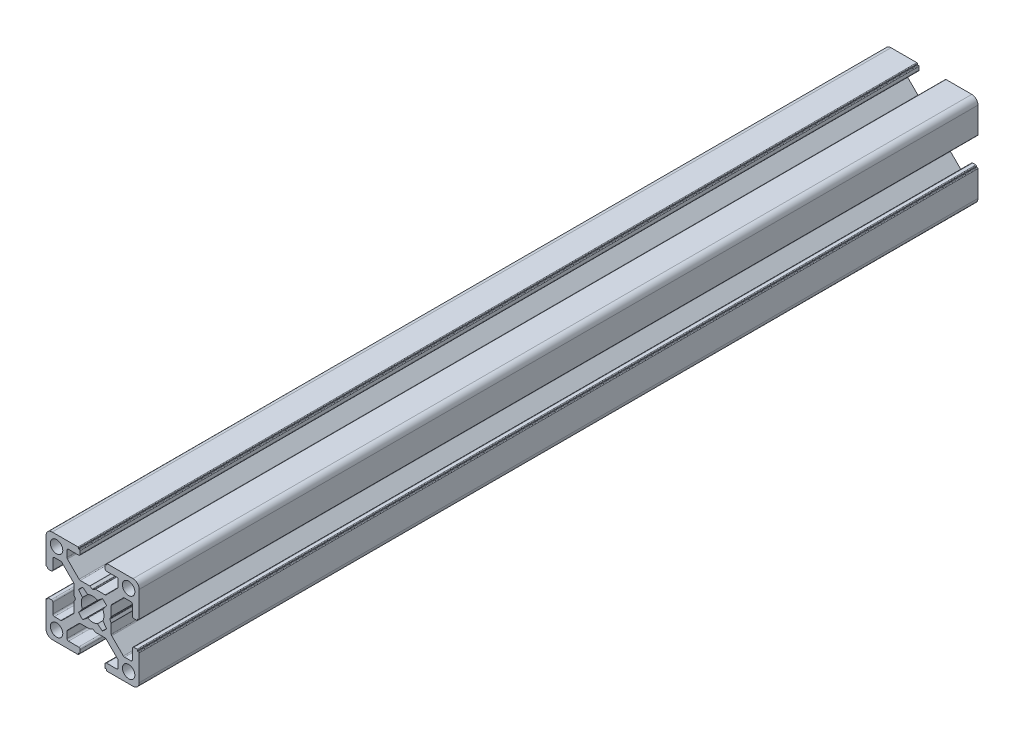
SolidWorks part; units mm, degrees
ref_plane "Alzado" through (0, 0, 0) normal (0, 0, 1) x (1, 0, 0)
ref_plane "Planta" through (0, 0, 0) normal (0, 1, 0) x (1, 0, 0)
ref_plane "Vista lateral" through (0, 0, 0) normal (1, 0, 0) x (0, 0, -1)
ref_plane "Plano1" through (0, 0, 1000) normal (0, 0, 1) x (1, 0, 0)
sketch "Croquis1" plane through (0, 0, 1000) normal (0, 0, 1) x (1, 0, 0)
  line L16 (-7.8359, -10.4816) -> (-6.3001, -11.7194)
  line L17 (-3.0999, -11.7194) -> (-1.5641, -10.4816)
  line L18 (-0.1947, -11.8453) -> (-1.4194, -13.3999)
  line L19 (-1.4194, -16.6001) -> (-0.1947, -18.1547)
  line L20 (-1.5641, -19.5184) -> (-3.0999, -18.2806)
  line L21 (-6.3001, -18.2806) -> (-7.8359, -19.5184)
  line L22 (-9.2053, -18.1547) -> (-7.9806, -16.6001)
  line L23 (-7.9806, -13.3999) -> (-9.2053, -11.8453)
  line L24 (9.8, -10.5) -> (10.1, -10.5)
  line L25 (10.3, -10.3) -> (10.3, -2)
  line L26 (8.3, 0) -> (0, 0)
  line L27 (-0.2, -0.2) -> (-0.2, -0.5)
  line L28 (-0.2, -0.5) -> (-0.5, -0.5)
  line L29 (-0.7, -0.7) -> (-0.7, -1.7)
  line L30 (-0.2, -2.2) -> (3.05, -2.2)
  line L31 (3.55, -2.7) -> (3.55, -4.7431)
  line L32 (3.4037, -5.0964) -> (-0.3491, -8.8534)
  line L33 (-0.7028, -9) -> (-3.7468, -9)
  line L34 (-3.8462, -9.0264) -> (-4.6006, -9.4583)
  line L35 (-4.7994, -9.4583) -> (-5.5538, -9.0264)
  line L36 (-5.6532, -9) -> (-8.6972, -9)
  line L37 (-9.0509, -8.8534) -> (-12.8037, -5.0964)
  line L38 (-12.95, -4.7431) -> (-12.95, -2.7)
  line L39 (-12.45, -2.2) -> (-9.2, -2.2)
  line L40 (-8.7, -1.7) -> (-8.7, -0.7)
  line L41 (-8.9, -0.5) -> (-9.2, -0.5)
  line L42 (-9.2, -0.5) -> (-9.2, -0.2)
  line L43 (-9.4, 0) -> (-17.7, 0)
  line L44 (-19.7, -2) -> (-19.7, -10.3)
  line L45 (-19.5, -10.5) -> (-19.2, -10.5)
  line L46 (-19.2, -10.5) -> (-19.2, -10.8)
  line L47 (-19, -11) -> (-18, -11)
  line L48 (-17.5, -10.5) -> (-17.5, -7.25)
  line L49 (-17, -6.75) -> (-14.9569, -6.75)
  line L50 (-14.6036, -6.8963) -> (-10.8466, -10.6491)
  line L51 (-10.7, -11.0028) -> (-10.7, -14.0468)
  line L52 (-10.6736, -14.1462) -> (-10.2417, -14.9006)
  line L53 (-10.2417, -15.0994) -> (-10.6736, -15.8538)
  line L54 (-10.7, -15.9532) -> (-10.7, -18.9972)
  line L55 (-10.8466, -19.3509) -> (-14.6036, -23.1037)
  line L56 (-14.9569, -23.25) -> (-17, -23.25)
  line L57 (-17.5, -22.75) -> (-17.5, -19.5)
  line L58 (-18, -19) -> (-19, -19)
  line L59 (-19.2, -19.2) -> (-19.2, -19.5)
  line L60 (-19.2, -19.5) -> (-19.5, -19.5)
  line L61 (-19.7, -19.7) -> (-19.7, -28)
  line L62 (-17.7, -30) -> (-9.4, -30)
  line L63 (-9.2, -29.8) -> (-9.2, -29.5)
  line L64 (-9.2, -29.5) -> (-8.9, -29.5)
  line L65 (-8.7, -29.3) -> (-8.7, -28.3)
  line L66 (-9.2, -27.8) -> (-12.45, -27.8)
  line L67 (-12.95, -27.3) -> (-12.95, -25.2569)
  line L68 (-12.8037, -24.9036) -> (-9.0509, -21.1466)
  line L69 (-8.6972, -21) -> (-5.6532, -21)
  line L70 (-5.5538, -20.9736) -> (-4.7994, -20.5417)
  line L71 (-4.6006, -20.5417) -> (-3.8462, -20.9736)
  line L72 (-3.7468, -21) -> (-0.7028, -21)
  line L73 (-0.3491, -21.1466) -> (3.4037, -24.9036)
  line L74 (3.55, -25.2569) -> (3.55, -27.3)
  line L75 (3.05, -27.8) -> (-0.2, -27.8)
  line L76 (-0.7, -28.3) -> (-0.7, -29.3)
  line L77 (-0.5, -29.5) -> (-0.2, -29.5)
  line L78 (-0.2, -29.5) -> (-0.2, -29.8)
  line L79 (0, -30) -> (8.3, -30)
  line L80 (10.3, -28) -> (10.3, -19.7)
  line L81 (10.1, -19.5) -> (9.8, -19.5)
  line L82 (9.8, -19.5) -> (9.8, -19.2)
  line L83 (9.6, -19) -> (8.6, -19)
  line L84 (8.1, -19.5) -> (8.1, -22.75)
  line L85 (7.6, -23.25) -> (5.5569, -23.25)
  line L86 (5.2036, -23.1037) -> (1.4466, -19.3509)
  line L87 (1.3, -18.9972) -> (1.3, -15.9532)
  line L88 (1.2736, -15.8538) -> (0.8417, -15.0994)
  line L89 (0.8417, -14.9006) -> (1.2736, -14.1462)
  line L90 (1.3, -14.0468) -> (1.3, -11.0028)
  line L91 (1.4466, -10.6491) -> (5.2036, -6.8963)
  line L92 (5.5569, -6.75) -> (7.6, -6.75)
  line L93 (8.1, -7.25) -> (8.1, -10.5)
  line L94 (8.6, -11) -> (9.6, -11)
  line L95 (9.8, -10.8) -> (9.8, -10.5)
  line L96 (8, -2.3) -> (5.8, -4.5) construction
  line L97 (-15.2, -2.3) -> (-17.4, -4.5) construction
  line L98 (-4.7, -15) -> (6.9, -15) construction
  arc A16 (-9.2053, -11.8453) -> (-7.8359, -10.4816) centre (-4.7, -15) cw
  arc A17 (-6.3001, -11.7194) -> (-3.0999, -11.7194) centre (-4.7, -15) cw
  arc A18 (-1.5641, -10.4816) -> (-0.1947, -11.8453) centre (-4.7, -15) cw
  arc A19 (-1.4194, -13.3999) -> (-1.4194, -16.6001) centre (-4.7, -15) cw
  arc A20 (-0.1947, -18.1547) -> (-1.5641, -19.5184) centre (-4.7, -15) cw
  arc A21 (-3.0999, -18.2806) -> (-6.3001, -18.2806) centre (-4.7, -15) cw
  arc A22 (-7.8359, -19.5184) -> (-9.2053, -18.1547) centre (-4.7, -15) cw
  arc A23 (-7.9806, -16.6001) -> (-7.9806, -13.3999) centre (-4.7, -15) cw
  arc A24 (10.1, -10.5) -> (10.3, -10.3) centre (10.1, -10.3) ccw
  arc A25 (10.3, -2) -> (8.3, 0) centre (8.3, -2) ccw
  arc A26 (0, 0) -> (-0.2, -0.2) centre (0, -0.2) ccw
  arc A27 (-0.5, -0.5) -> (-0.7, -0.7) centre (-0.5, -0.7) ccw
  arc A28 (-0.7, -1.7) -> (-0.2, -2.2) centre (-0.2, -1.7) ccw
  arc A29 (3.05, -2.2) -> (3.55, -2.7) centre (3.05, -2.7) cw
  arc A30 (3.55, -4.7431) -> (3.4037, -5.0964) centre (3.05, -4.7431) cw
  arc A31 (-0.3491, -8.8534) -> (-0.7028, -9) centre (-0.7028, -8.5) cw
  arc A32 (-3.7468, -9) -> (-3.8462, -9.0264) centre (-3.7468, -9.2) ccw
  arc A33 (-4.6006, -9.4583) -> (-4.7994, -9.4583) centre (-4.7, -9.2847) cw
  arc A34 (-5.5538, -9.0264) -> (-5.6532, -9) centre (-5.6532, -9.2) ccw
  arc A35 (-8.6972, -9) -> (-9.0509, -8.8534) centre (-8.6972, -8.5) cw
  arc A36 (-12.8037, -5.0964) -> (-12.95, -4.7431) centre (-12.45, -4.7431) cw
  arc A37 (-12.95, -2.7) -> (-12.45, -2.2) centre (-12.45, -2.7) cw
  arc A38 (-9.2, -2.2) -> (-8.7, -1.7) centre (-9.2, -1.7) ccw
  arc A39 (-8.7, -0.7) -> (-8.9, -0.5) centre (-8.9, -0.7) ccw
  arc A40 (-9.2, -0.2) -> (-9.4, 0) centre (-9.4, -0.2) ccw
  arc A41 (-17.7, 0) -> (-19.7, -2) centre (-17.7, -2) ccw
  arc A42 (-19.7, -10.3) -> (-19.5, -10.5) centre (-19.5, -10.3) ccw
  arc A43 (-19.2, -10.8) -> (-19, -11) centre (-19, -10.8) ccw
  arc A44 (-18, -11) -> (-17.5, -10.5) centre (-18, -10.5) ccw
  arc A45 (-17.5, -7.25) -> (-17, -6.75) centre (-17, -7.25) cw
  arc A46 (-14.9569, -6.75) -> (-14.6036, -6.8963) centre (-14.9569, -7.25) cw
  arc A47 (-10.8466, -10.6491) -> (-10.7, -11.0028) centre (-11.2, -11.0028) cw
  arc A48 (-10.7, -14.0468) -> (-10.6736, -14.1462) centre (-10.5, -14.0468) ccw
  arc A49 (-10.2417, -14.9006) -> (-10.2417, -15.0994) centre (-10.4153, -15) cw
  arc A50 (-10.6736, -15.8538) -> (-10.7, -15.9532) centre (-10.5, -15.9532) ccw
  arc A51 (-10.7, -18.9972) -> (-10.8466, -19.3509) centre (-11.2, -18.9972) cw
  arc A52 (-14.6036, -23.1037) -> (-14.9569, -23.25) centre (-14.9569, -22.75) cw
  arc A53 (-17, -23.25) -> (-17.5, -22.75) centre (-17, -22.75) cw
  arc A54 (-17.5, -19.5) -> (-18, -19) centre (-18, -19.5) ccw
  arc A55 (-19, -19) -> (-19.2, -19.2) centre (-19, -19.2) ccw
  arc A56 (-19.5, -19.5) -> (-19.7, -19.7) centre (-19.5, -19.7) ccw
  arc A57 (-19.7, -28) -> (-17.7, -30) centre (-17.7, -28) ccw
  arc A58 (-9.4, -30) -> (-9.2, -29.8) centre (-9.4, -29.8) ccw
  arc A59 (-8.9, -29.5) -> (-8.7, -29.3) centre (-8.9, -29.3) ccw
  arc A60 (-8.7, -28.3) -> (-9.2, -27.8) centre (-9.2, -28.3) ccw
  arc A61 (-12.45, -27.8) -> (-12.95, -27.3) centre (-12.45, -27.3) cw
  arc A62 (-12.95, -25.2569) -> (-12.8037, -24.9036) centre (-12.45, -25.2569) cw
  arc A63 (-9.0509, -21.1466) -> (-8.6972, -21) centre (-8.6972, -21.5) cw
  arc A64 (-5.6532, -21) -> (-5.5538, -20.9736) centre (-5.6532, -20.8) ccw
  arc A65 (-4.7994, -20.5417) -> (-4.6006, -20.5417) centre (-4.7, -20.7153) cw
  arc A66 (-3.8462, -20.9736) -> (-3.7468, -21) centre (-3.7468, -20.8) ccw
  arc A67 (-0.7028, -21) -> (-0.3491, -21.1466) centre (-0.7028, -21.5) cw
  arc A68 (3.4037, -24.9036) -> (3.55, -25.2569) centre (3.05, -25.2569) cw
  arc A69 (3.55, -27.3) -> (3.05, -27.8) centre (3.05, -27.3) cw
  arc A70 (-0.2, -27.8) -> (-0.7, -28.3) centre (-0.2, -28.3) ccw
  arc A71 (-0.7, -29.3) -> (-0.5, -29.5) centre (-0.5, -29.3) ccw
  arc A72 (-0.2, -29.8) -> (0, -30) centre (0, -29.8) ccw
  arc A73 (8.3, -30) -> (10.3, -28) centre (8.3, -28) ccw
  arc A74 (10.3, -19.7) -> (10.1, -19.5) centre (10.1, -19.7) ccw
  arc A75 (9.8, -19.2) -> (9.6, -19) centre (9.6, -19.2) ccw
  arc A76 (8.6, -19) -> (8.1, -19.5) centre (8.6, -19.5) ccw
  arc A77 (8.1, -22.75) -> (7.6, -23.25) centre (7.6, -22.75) cw
  arc A78 (5.5569, -23.25) -> (5.2036, -23.1037) centre (5.5569, -22.75) cw
  arc A79 (1.4466, -19.3509) -> (1.3, -18.9972) centre (1.8, -18.9972) cw
  arc A80 (1.3, -15.9532) -> (1.2736, -15.8538) centre (1.1, -15.9532) ccw
  arc A81 (0.8417, -15.0994) -> (0.8417, -14.9006) centre (1.0153, -15) cw
  arc A82 (1.2736, -14.1462) -> (1.3, -14.0468) centre (1.1, -14.0468) ccw
  arc A83 (1.3, -11.0028) -> (1.4466, -10.6491) centre (1.8, -11.0028) cw
  arc A84 (5.2036, -6.8963) -> (5.5569, -6.75) centre (5.5569, -7.25) cw
  arc A85 (7.6, -6.75) -> (8.1, -7.25) centre (7.6, -7.25) cw
  arc A86 (8.1, -10.5) -> (8.6, -11) centre (8.6, -10.5) ccw
  arc A87 (9.6, -11) -> (9.8, -10.8) centre (9.6, -10.8) ccw
  circle A88 centre (-16.3, -3.4) radius 2
  circle A89 centre (6.9, -3.4) radius 2
  circle A90 centre (-16.3, -26.6) radius 2
  circle A91 centre (6.9, -26.6) radius 2
  dimension "D3" = 4
  dimension "D1" = 30
  dimension "D2" = 30
  dimension "D4" = 23.2
  dimension "D5" = 23.2
extrude "Saliente-Extruir1" add sketch "Croquis1" against normal blind 270
